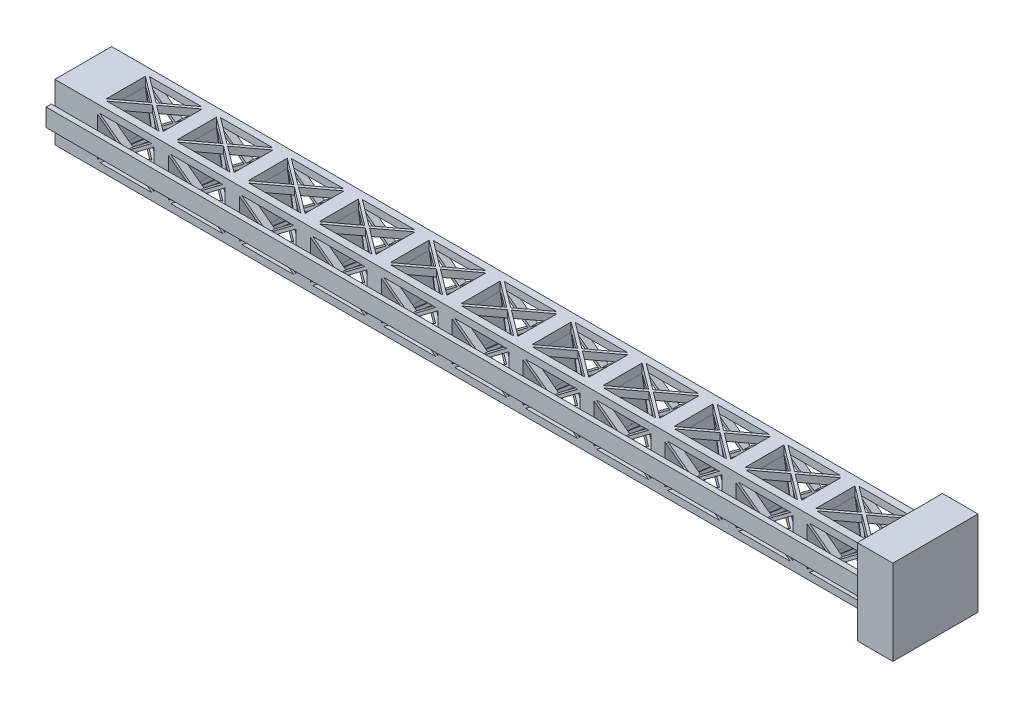
SolidWorks part; units mm, degrees
material "Cast Alloy Steel"
ref_plane "Front Plane" through (0, 0, 0) normal (0, 0, 1) x (1, 0, 0)
ref_plane "Top Plane" through (0, 0, 0) normal (0, 1, 0) x (1, 0, 0)
ref_plane "Right Plane" through (0, 0, 0) normal (1, 0, 0) x (0, 0, -1)
sketch "Sketch2" plane through (0, 0, 0) normal (0, 0, 1) x (1, 0, 0)
  line L1 (-1524, 101.6) -> (1524, 101.6)
  line L2 (-1524, 101.6) -> (-1524, -101.6)
  line L3 (-1524, -101.6) -> (1524, -101.6)
  line L4 (1524, 101.6) -> (1524, -101.6)
  line L5 (-1524, 101.6) -> (1524, -101.6) construction
  line L6 (-1524, -101.6) -> (1524, 101.6) construction
  point P0 (0, 0)
  dimension "D1" = 3048
  dimension "D2" = 203.2
extrude "Boss-Extrude1" add sketch "Sketch2" against normal blind 203.2
sketch "Sketch6" plane through (0, 0, -203.2) normal (0, 0, -1) x (-1, 0, 0)
  line L0 (-93.1333, 76.2) -> (0, 6.35)
  line L1 (-93.1333, -76.2) -> (93.1333, -76.2)
  line L2 (-101.6, -69.85) -> (-101.6, 69.85)
  line L3 (-93.1333, 76.2) -> (93.1333, 76.2)
  line L4 (101.6, -69.85) -> (101.6, 69.85)
  line L5 (0, 6.35) -> (93.1333, 76.2)
  line L7 (-101.6, 69.85) -> (-8.4667, 0)
  line L8 (-101.6, -69.85) -> (-8.4667, 0)
  line L9 (101.6, 69.85) -> (8.4667, 0)
  line L10 (0, -6.35) -> (93.1333, -76.2)
  line L12 (8.4667, 0) -> (101.6, -69.85)
  line L13 (0, -6.35) -> (-93.1333, -76.2)
  point P0 (0, 0)
extrude "Cut-Extrude6" cut sketch "Sketch6" against normal blind 203.2
sketch "Sketch8" plane through (0, 101.6, 0) normal (0, 1, 0) x (1, 0, 0)
  line L0 (-93.1186, 177.9517) -> (0.0147, 108.1017)
  line L1 (-93.1186, 25.5517) -> (93.148, 25.5517)
  line L2 (-101.5853, 31.9017) -> (-101.5853, 171.6017)
  line L3 (-93.1186, 177.9517) -> (93.148, 177.9517)
  line L4 (101.6147, 31.9017) -> (101.6147, 171.6017)
  line L5 (0.0147, 108.1017) -> (93.148, 177.9517)
  line L7 (-101.5853, 171.6017) -> (-8.452, 101.7517)
  line L8 (-101.5853, 31.9017) -> (-8.452, 101.7517)
  line L9 (101.6147, 171.6017) -> (8.4814, 101.7517)
  line L10 (0.0147, 95.4017) -> (93.148, 25.5517)
  line L12 (8.4814, 101.7517) -> (101.6147, 31.9017)
  line L13 (0.0147, 95.4017) -> (-93.1186, 25.5517)
  point P0 (0.0147, 101.7517)
extrude "Cut-Extrude7" cut sketch "Sketch8" against normal blind 203.2
pattern_linear "LPattern4" count 6 spacing 254 along (-1, 0, 0) count 6 spacing 254 along (1, 0, 0) of "Cut-Extrude6"
pattern_linear "LPattern5" count 6 spacing 254 along (1, 0, 0) count 6 spacing 254 along (-1, 0, 0) of "Cut-Extrude7"
sketch "Sketch10" plane through (1524, 0, 0) normal (1, 0, 0) x (0, 0, -1)
  line L1 (-50.8, -152.4) -> (254, -152.4)
  line L2 (-50.8, -152.4) -> (-50.8, 152.4)
  line L3 (-50.8, 152.4) -> (254, 152.4)
  line L4 (254, -152.4) -> (254, 152.4)
  line L5 (-50.8, -152.4) -> (254, 152.4) construction
  line L6 (-50.8, 152.4) -> (254, -152.4) construction
  point P0 (101.6, 0)
  dimension "D1" = 101.6
  dimension "D2" = 101.6
  dimension "D3" = 304.8
  dimension "D4" = 304.8
extrude "Boss-Extrude2" add sketch "Sketch10" along normal blind 127 from offset 124.46 offset against normal yes
sketch "Sketch11" plane through (-1524, 0, 0) normal (-1, 0, 0) x (0, 0, 1)
  line L0 (12.8178, 31.75) -> (12.8178, 12.8178)
  line L1 (12.8178, -31.75) -> (31.75, -31.75)
  line L3 (12.8178, 31.75) -> (31.75, 31.75)
  line L4 (31.75, -31.75) -> (31.75, 31.75)
  line L7 (12.8178, 12.8178) -> (0, 12.8178)
  line L8 (12.8178, -31.75) -> (12.8178, -12.8178)
  line L9 (12.8178, -12.8178) -> (0, -12.8178)
  line L10 (0, 12.8178) -> (0, -12.8178)
  line L11 (0, 101.6) -> (0, -101.6) construction
  point P0 (0, 0)
extrude "Boss-Extrude3" add sketch "Sketch11" along direction (-1, 0, 0) on the side against the normal up to surface (2923.54 mm away)
